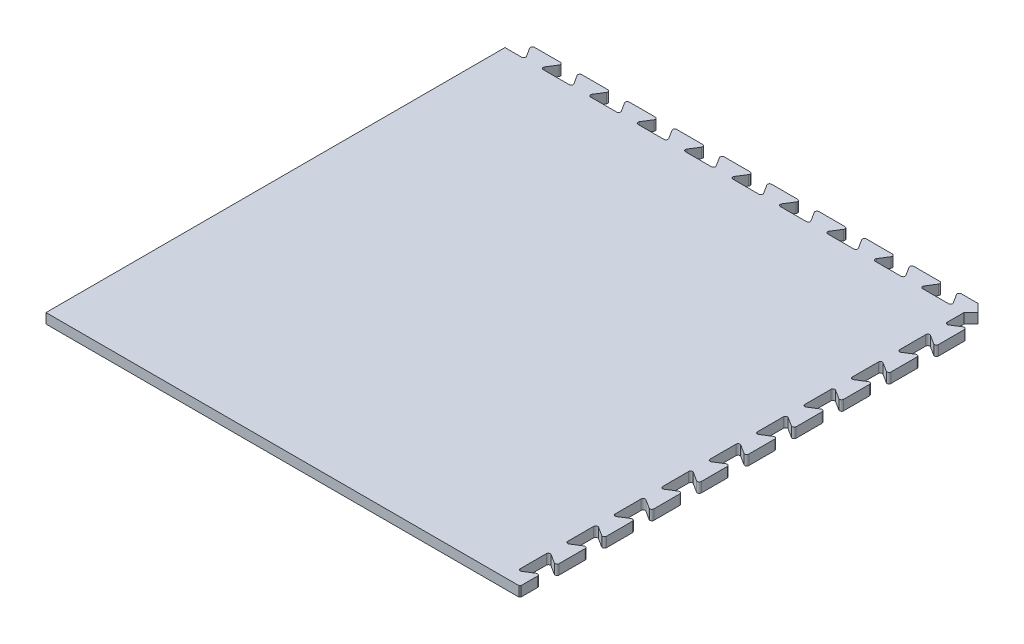
SolidWorks part; units mm, degrees
ref_plane "Front Plane" through (0, 0, 0) normal (0, 0, 1) x (1, 0, 0)
ref_plane "Top Plane" through (0, 0, 0) normal (0, 1, 0) x (1, 0, 0)
ref_plane "Right Plane" through (0, 0, 0) normal (1, 0, 0) x (0, 0, -1)
ref_plane "Plane1" through (0, 12.7, 0) normal (0, 1, 0) x (1, 0, 0)
sketch "Sketch1" plane through (0, 12.7, 0) normal (0, 1, 0) x (1, 0, 0)
  line L0 (-270.6042, 291.8914) -> (-291.8914, 291.8914)
  line L1 (-291.8914, 291.8914) -> (-291.8914, -291.8914)
  line L2 (-291.8914, -291.8914) -> (309.7858, -291.8914)
  line L3 (309.7858, -291.8914) -> (310.9414, -290.7358)
  line L4 (310.9414, -290.7358) -> (310.9414, -269.4633)
  line L5 (307.0392, -267.3194) -> (295.7935, -274.4647)
  line L6 (291.8914, -272.3208) -> (291.8914, -239.3008)
  line L7 (295.7935, -237.1569) -> (307.0392, -244.3022)
  line L8 (310.9414, -242.1583) -> (310.9414, -209.1383)
  line L9 (307.0392, -206.9944) -> (295.7935, -214.1397)
  line L10 (291.8914, -211.9958) -> (291.8914, -178.9758)
  line L11 (295.7935, -176.8319) -> (307.0392, -183.9772)
  line L12 (310.9414, -181.8333) -> (310.9414, -148.8133)
  line L13 (307.0392, -146.6694) -> (295.7935, -153.8147)
  line L14 (291.8914, -151.6708) -> (291.8914, -118.6508)
  line L15 (295.7935, -116.5069) -> (307.0392, -123.6522)
  line L16 (310.9414, -121.5083) -> (310.9414, -88.4883)
  line L17 (307.0392, -86.3444) -> (295.7935, -93.4897)
  line L18 (291.8914, -91.3458) -> (291.8914, -58.3258)
  line L19 (295.7935, -56.1819) -> (307.0392, -63.3272)
  line L20 (310.9414, -61.1833) -> (310.9414, -28.1633)
  line L21 (307.0392, -26.0194) -> (295.7935, -33.1647)
  line L22 (291.8914, -31.0208) -> (291.8914, 1.9992)
  line L23 (295.7935, 4.1431) -> (307.0392, -3.0022)
  line L24 (310.9414, -0.8583) -> (310.9414, 32.1617)
  line L25 (307.0392, 34.3056) -> (295.7935, 27.1603)
  line L26 (291.8914, 29.3042) -> (291.8914, 62.3242)
  line L27 (295.7935, 64.4681) -> (307.0392, 57.3228)
  line L28 (310.9414, 59.4667) -> (310.9414, 92.4867)
  line L29 (307.0392, 94.6306) -> (295.7935, 87.4853)
  line L30 (291.8914, 89.6292) -> (291.8914, 122.6492)
  line L31 (295.7935, 124.7931) -> (307.0392, 117.6478)
  line L32 (310.9414, 119.7917) -> (310.9414, 152.8117)
  line L33 (307.0392, 154.9556) -> (295.7935, 147.8103)
  line L34 (291.8914, 149.9542) -> (291.8914, 182.9742)
  line L35 (295.7935, 185.1181) -> (307.0392, 177.9728)
  line L36 (310.9414, 180.1167) -> (310.9414, 213.1367)
  line L37 (307.0392, 215.2806) -> (295.7935, 208.1353)
  line L38 (291.8914, 210.2792) -> (291.8914, 243.2992)
  line L39 (295.7935, 245.4431) -> (307.0392, 238.2978)
  line L40 (310.9414, 240.4417) -> (310.9414, 273.4617)
  line L41 (307.0392, 275.6056) -> (295.7935, 268.4603)
  line L42 (291.8914, 270.6042) -> (291.8914, 291.8914)
  line L43 (291.8914, 291.8914) -> (300.8386, 300.8386)
  line L44 (300.8386, 300.8386) -> (290.7358, 310.9414)
  line L45 (290.7358, 310.9414) -> (269.4633, 310.9414)
  line L46 (267.3194, 307.0392) -> (274.4647, 295.7935)
  line L47 (272.3208, 291.8914) -> (239.3008, 291.8914)
  line L48 (237.1569, 295.7935) -> (244.3022, 307.0392)
  line L49 (242.1583, 310.9414) -> (209.1383, 310.9414)
  line L50 (206.9944, 307.0392) -> (214.1397, 295.7935)
  line L51 (211.9958, 291.8914) -> (178.9758, 291.8914)
  line L52 (176.8319, 295.7935) -> (183.9772, 307.0392)
  line L53 (181.8333, 310.9414) -> (148.8133, 310.9414)
  line L54 (146.6694, 307.0392) -> (153.8147, 295.7935)
  line L55 (151.6708, 291.8914) -> (118.6508, 291.8914)
  line L56 (116.5069, 295.7935) -> (123.6522, 307.0392)
  line L57 (121.5083, 310.9414) -> (88.4883, 310.9414)
  line L58 (86.3444, 307.0392) -> (93.4897, 295.7935)
  line L59 (91.3458, 291.8914) -> (58.3258, 291.8914)
  line L60 (56.1819, 295.7935) -> (63.3272, 307.0392)
  line L61 (61.1833, 310.9414) -> (28.1633, 310.9414)
  line L62 (26.0194, 307.0392) -> (33.1647, 295.7935)
  line L63 (31.0208, 291.8914) -> (-1.9992, 291.8914)
  line L64 (-4.1431, 295.7935) -> (3.0022, 307.0392)
  line L65 (0.8583, 310.9414) -> (-32.1617, 310.9414)
  line L66 (-34.3056, 307.0392) -> (-27.1603, 295.7935)
  line L67 (-29.3042, 291.8914) -> (-62.3242, 291.8914)
  line L68 (-64.4681, 295.7935) -> (-57.3228, 307.0392)
  line L69 (-59.4667, 310.9414) -> (-92.4867, 310.9414)
  line L70 (-94.6306, 307.0392) -> (-87.4853, 295.7935)
  line L71 (-89.6292, 291.8914) -> (-122.6492, 291.8914)
  line L72 (-124.7931, 295.7935) -> (-117.6478, 307.0392)
  line L73 (-119.7917, 310.9414) -> (-152.8117, 310.9414)
  line L74 (-154.9556, 307.0392) -> (-147.8103, 295.7935)
  line L75 (-149.9542, 291.8914) -> (-182.9742, 291.8914)
  line L76 (-185.1181, 295.7935) -> (-177.9728, 307.0392)
  line L77 (-180.1167, 310.9414) -> (-213.1367, 310.9414)
  line L78 (-215.2806, 307.0392) -> (-208.1353, 295.7935)
  line L79 (-210.2792, 291.8914) -> (-243.2992, 291.8914)
  line L80 (-245.4431, 295.7935) -> (-238.2978, 307.0392)
  line L81 (-240.4417, 310.9414) -> (-273.4617, 310.9414)
  line L82 (-275.6056, 307.0392) -> (-268.4603, 295.7935)
  arc A0 (310.9414, -269.4633) -> (307.0392, -267.3194) centre (308.4014, -269.4633) ccw
  arc A1 (295.7935, -274.4647) -> (291.8914, -272.3208) centre (294.4314, -272.3208) cw
  arc A2 (291.8914, -239.3008) -> (295.7935, -237.1569) centre (294.4314, -239.3008) cw
  arc A3 (307.0392, -244.3022) -> (310.9414, -242.1583) centre (308.4014, -242.1583) ccw
  arc A4 (310.9414, -209.1383) -> (307.0392, -206.9944) centre (308.4014, -209.1383) ccw
  arc A5 (295.7935, -214.1397) -> (291.8914, -211.9958) centre (294.4314, -211.9958) cw
  arc A6 (291.8914, -178.9758) -> (295.7935, -176.8319) centre (294.4314, -178.9758) cw
  arc A7 (307.0392, -183.9772) -> (310.9414, -181.8333) centre (308.4014, -181.8333) ccw
  arc A8 (310.9414, -148.8133) -> (307.0392, -146.6694) centre (308.4014, -148.8133) ccw
  arc A9 (295.7935, -153.8147) -> (291.8914, -151.6708) centre (294.4314, -151.6708) cw
  arc A10 (291.8914, -118.6508) -> (295.7935, -116.5069) centre (294.4314, -118.6508) cw
  arc A11 (307.0392, -123.6522) -> (310.9414, -121.5083) centre (308.4014, -121.5083) ccw
  arc A12 (310.9414, -88.4883) -> (307.0392, -86.3444) centre (308.4014, -88.4883) ccw
  arc A13 (295.7935, -93.4897) -> (291.8914, -91.3458) centre (294.4314, -91.3458) cw
  arc A14 (291.8914, -58.3258) -> (295.7935, -56.1819) centre (294.4314, -58.3258) cw
  arc A15 (307.0392, -63.3272) -> (310.9414, -61.1833) centre (308.4014, -61.1833) ccw
  arc A16 (310.9414, -28.1633) -> (307.0392, -26.0194) centre (308.4014, -28.1633) ccw
  arc A17 (295.7935, -33.1647) -> (291.8914, -31.0208) centre (294.4314, -31.0208) cw
  arc A18 (291.8914, 1.9992) -> (295.7935, 4.1431) centre (294.4314, 1.9992) cw
  arc A19 (307.0392, -3.0022) -> (310.9414, -0.8583) centre (308.4014, -0.8583) ccw
  arc A20 (310.9414, 32.1617) -> (307.0392, 34.3056) centre (308.4014, 32.1617) ccw
  arc A21 (295.7935, 27.1603) -> (291.8914, 29.3042) centre (294.4314, 29.3042) cw
  arc A22 (291.8914, 62.3242) -> (295.7935, 64.4681) centre (294.4314, 62.3242) cw
  arc A23 (307.0392, 57.3228) -> (310.9414, 59.4667) centre (308.4014, 59.4667) ccw
  arc A24 (310.9414, 92.4867) -> (307.0392, 94.6306) centre (308.4014, 92.4867) ccw
  arc A25 (295.7935, 87.4853) -> (291.8914, 89.6292) centre (294.4314, 89.6292) cw
  arc A26 (291.8914, 122.6492) -> (295.7935, 124.7931) centre (294.4314, 122.6492) cw
  arc A27 (307.0392, 117.6478) -> (310.9414, 119.7917) centre (308.4014, 119.7917) ccw
  arc A28 (310.9414, 152.8117) -> (307.0392, 154.9556) centre (308.4014, 152.8117) ccw
  arc A29 (295.7935, 147.8103) -> (291.8914, 149.9542) centre (294.4314, 149.9542) cw
  arc A30 (291.8914, 182.9742) -> (295.7935, 185.1181) centre (294.4314, 182.9742) cw
  arc A31 (307.0392, 177.9728) -> (310.9414, 180.1167) centre (308.4014, 180.1167) ccw
  arc A32 (310.9414, 213.1367) -> (307.0392, 215.2806) centre (308.4014, 213.1367) ccw
  arc A33 (295.7935, 208.1353) -> (291.8914, 210.2792) centre (294.4314, 210.2792) cw
  arc A34 (291.8914, 243.2992) -> (295.7935, 245.4431) centre (294.4314, 243.2992) cw
  arc A35 (307.0392, 238.2978) -> (310.9414, 240.4417) centre (308.4014, 240.4417) ccw
  arc A36 (310.9414, 273.4617) -> (307.0392, 275.6056) centre (308.4014, 273.4617) ccw
  arc A37 (295.7935, 268.4603) -> (291.8914, 270.6042) centre (294.4314, 270.6042) cw
  arc A38 (269.4633, 310.9414) -> (267.3194, 307.0392) centre (269.4633, 308.4014) ccw
  arc A39 (274.4647, 295.7935) -> (272.3208, 291.8914) centre (272.3208, 294.4314) cw
  arc A40 (239.3008, 291.8914) -> (237.1569, 295.7935) centre (239.3008, 294.4314) cw
  arc A41 (244.3022, 307.0392) -> (242.1583, 310.9414) centre (242.1583, 308.4014) ccw
  arc A42 (209.1383, 310.9414) -> (206.9944, 307.0392) centre (209.1383, 308.4014) ccw
  arc A43 (214.1397, 295.7935) -> (211.9958, 291.8914) centre (211.9958, 294.4314) cw
  arc A44 (178.9758, 291.8914) -> (176.8319, 295.7935) centre (178.9758, 294.4314) cw
  arc A45 (183.9772, 307.0392) -> (181.8333, 310.9414) centre (181.8333, 308.4014) ccw
  arc A46 (148.8133, 310.9414) -> (146.6694, 307.0392) centre (148.8133, 308.4014) ccw
  arc A47 (153.8147, 295.7935) -> (151.6708, 291.8914) centre (151.6708, 294.4314) cw
  arc A48 (118.6508, 291.8914) -> (116.5069, 295.7935) centre (118.6508, 294.4314) cw
  arc A49 (123.6522, 307.0392) -> (121.5083, 310.9414) centre (121.5083, 308.4014) ccw
  arc A50 (88.4883, 310.9414) -> (86.3444, 307.0392) centre (88.4883, 308.4014) ccw
  arc A51 (93.4897, 295.7935) -> (91.3458, 291.8914) centre (91.3458, 294.4314) cw
  arc A52 (58.3258, 291.8914) -> (56.1819, 295.7935) centre (58.3258, 294.4314) cw
  arc A53 (63.3272, 307.0392) -> (61.1833, 310.9414) centre (61.1833, 308.4014) ccw
  arc A54 (28.1633, 310.9414) -> (26.0194, 307.0392) centre (28.1633, 308.4014) ccw
  arc A55 (33.1647, 295.7935) -> (31.0208, 291.8914) centre (31.0208, 294.4314) cw
  arc A56 (-1.9992, 291.8914) -> (-4.1431, 295.7935) centre (-1.9992, 294.4314) cw
  arc A57 (3.0022, 307.0392) -> (0.8583, 310.9414) centre (0.8583, 308.4014) ccw
  arc A58 (-32.1617, 310.9414) -> (-34.3056, 307.0392) centre (-32.1617, 308.4014) ccw
  arc A59 (-27.1603, 295.7935) -> (-29.3042, 291.8914) centre (-29.3042, 294.4314) cw
  arc A60 (-62.3242, 291.8914) -> (-64.4681, 295.7935) centre (-62.3242, 294.4314) cw
  arc A61 (-57.3228, 307.0392) -> (-59.4667, 310.9414) centre (-59.4667, 308.4014) ccw
  arc A62 (-92.4867, 310.9414) -> (-94.6306, 307.0392) centre (-92.4867, 308.4014) ccw
  arc A63 (-87.4853, 295.7935) -> (-89.6292, 291.8914) centre (-89.6292, 294.4314) cw
  arc A64 (-122.6492, 291.8914) -> (-124.7931, 295.7935) centre (-122.6492, 294.4314) cw
  arc A65 (-117.6478, 307.0392) -> (-119.7917, 310.9414) centre (-119.7917, 308.4014) ccw
  arc A66 (-152.8117, 310.9414) -> (-154.9556, 307.0392) centre (-152.8117, 308.4014) ccw
  arc A67 (-147.8103, 295.7935) -> (-149.9542, 291.8914) centre (-149.9542, 294.4314) cw
  arc A68 (-182.9742, 291.8914) -> (-185.1181, 295.7935) centre (-182.9742, 294.4314) cw
  arc A69 (-177.9728, 307.0392) -> (-180.1167, 310.9414) centre (-180.1167, 308.4014) ccw
  arc A70 (-213.1367, 310.9414) -> (-215.2806, 307.0392) centre (-213.1367, 308.4014) ccw
  arc A71 (-208.1353, 295.7935) -> (-210.2792, 291.8914) centre (-210.2792, 294.4314) cw
  arc A72 (-243.2992, 291.8914) -> (-245.4431, 295.7935) centre (-243.2992, 294.4314) cw
  arc A73 (-238.2978, 307.0392) -> (-240.4417, 310.9414) centre (-240.4417, 308.4014) ccw
  arc A74 (-273.4617, 310.9414) -> (-275.6056, 307.0392) centre (-273.4617, 308.4014) ccw
  arc A75 (-268.4603, 295.7935) -> (-270.6042, 291.8914) centre (-270.6042, 294.4314) cw
extrude "Boss-Extrude1" add sketch "Sketch1" against normal blind 12.7
